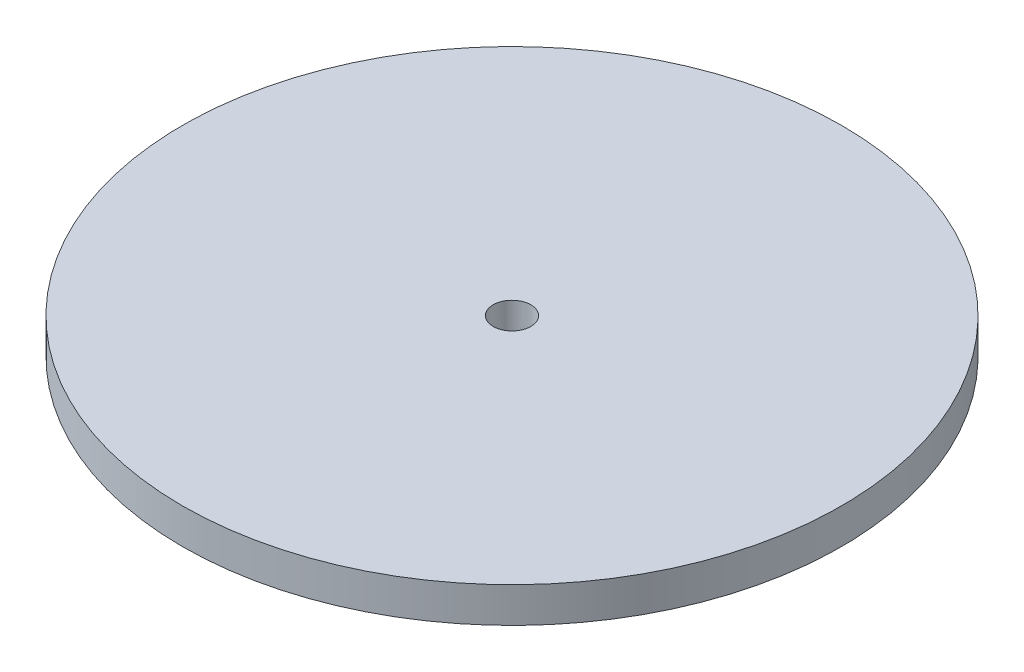
SolidWorks part; units mm, degrees
ref_plane "Front Plane" through (0, 0, 0) normal (0, 0, 1) x (1, 0, 0)
ref_plane "Top Plane" through (0, 0, 0) normal (0, 1, 0) x (1, 0, 0)
ref_plane "Right Plane" through (0, 0, 0) normal (1, 0, 0) x (0, 0, -1)
sketch "Sketch2" plane through (0, 0, 0) normal (0, 1, 0) x (1, 0, 0)
  circle A0 centre (0, 0) radius 140
  dimension "D1" = 280
extrude "Boss-Extrude1" add sketch "Sketch2" along normal blind 15
sketch "Sketch3" plane through (0, 15, 0) normal (0, 1, 0) x (1, 0, 0)
  circle A0 centre (0, 0) radius 8
  dimension "D1" = 16
extrude "Cut-Extrude1" cut sketch "Sketch3" against normal through all
